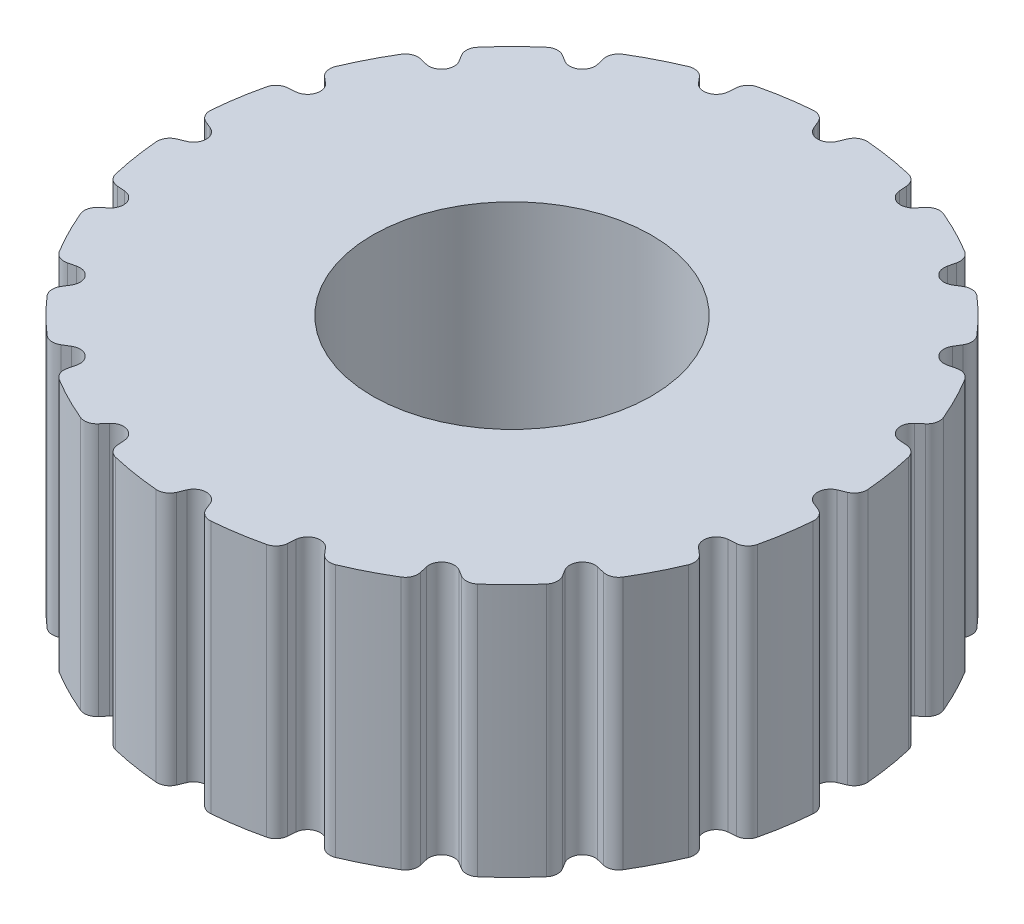
SolidWorks part; units mm, degrees
material "Alloy Steel"
ref_plane "Front Plane" through (0, 0, 0) normal (0, 0, 1) x (1, 0, 0)
ref_plane "Top Plane" through (0, 0, 0) normal (0, 1, 0) x (1, 0, 0)
ref_plane "Right Plane" through (0, 0, 0) normal (1, 0, 0) x (0, 0, -1)
sketch "Sketch1" plane through (0, 0, 0) normal (0, 1, 0) x (1, 0, 0)
  circle A0 centre (0, 0) radius 2.6
  circle A1 centre (0, 0) radius 1.1
  dimension "D1" = 5.2
  dimension "D2" = 2.2
extrude "Boss-Extrude1" add sketch "Sketch1" along normal blind 2
sketch "Sketch2" plane through (0, 0, 0) normal (0, 1, 0) x (1, 0, 0)
  line L0 (-0.145, 2.6) -> (0, 2.25)
  line L1 (0, 2.25) -> (0.145, 2.6)
  line L2 (0.145, 2.6) -> (-0.145, 2.6)
  circle A0 centre (0, 0) radius 2.6 construction
  circle A1 centre (0, 0) radius 2.25 construction
  point P2 (0, 2.6)
  point P7 (0, 0)
  dimension "D2" = 4.5
  dimension "D1" = 45
extrude "Cut-Extrude1" cut sketch "Sketch2" along normal through all
fillet "Fillet2" radius 0.1 3 edges at (0, 1, -2.25) (0.1433, 1, -2.596) (-0.1433, 1, -2.596)
pattern_circular "CirPattern1" count 20 over 360 about axis through (0, 0, 0) along (0, 1, 0) of "Cut-Extrude1", "Fillet2"
